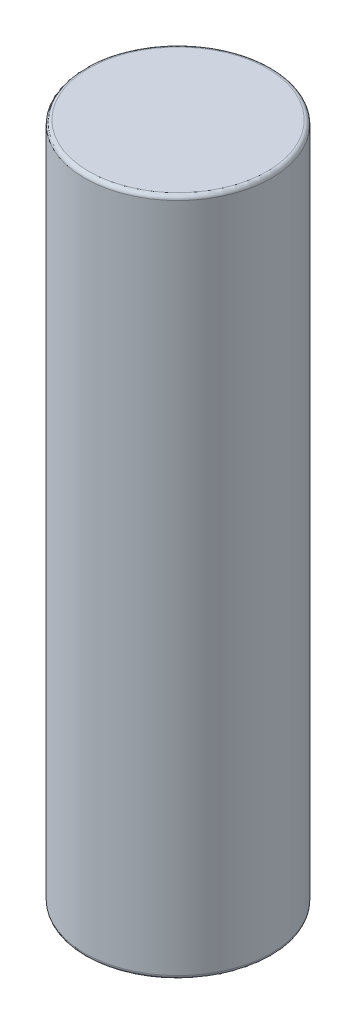
SolidWorks part; units mm, degrees
ref_plane "Front Plane" through (0, 0, 0) normal (0, 0, 1) x (1, 0, 0)
ref_plane "Top Plane" through (0, 0, 0) normal (0, 1, 0) x (1, 0, 0)
ref_plane "Right Plane" through (0, 0, 0) normal (1, 0, 0) x (0, 0, -1)
sketch "Sketch1" plane through (0, 0, 0) normal (0, 1, 0) x (1, 0, 0)
  circle A0 centre (0, 0) radius 7
extrude "Boss-Extrude1" add sketch "Sketch1" along normal blind 51
fillet "Fillet1" radius 0.3 2 edges at (0, 0, 7) (0, 51, 7)
